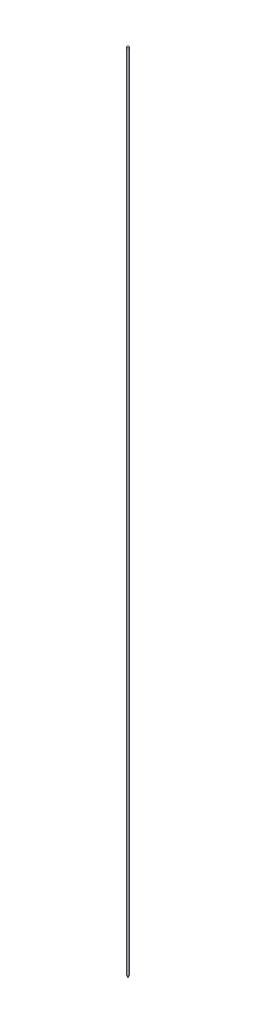
SolidWorks part; units mm, degrees
ref_plane "Alzado" through (0, 0, 0) normal (0, 0, 1) x (1, 0, 0)
ref_plane "Planta" through (0, 0, 0) normal (0, 1, 0) x (1, 0, 0)
ref_plane "Vista lateral" through (0, 0, 0) normal (1, 0, 0) x (0, 0, -1)
sketch "Croquis1" plane through (0, 0, 0) normal (0, 0, 1) x (1, 0, 0)
  line L0 (0, 11.2838) -> (0, -14.3611) construction
  line L1 (0, 138.1676) -> (1.5875, 138.1676)
  line L2 (1.5875, 138.1676) -> (1.5875, -987.2524)
  line L3 (0, -990.9565) -> (1.5875, -987.2524)
  line L4 (0, -990.9565) -> (0, 138.1676)
  dimension "D1" = 1.5875
  dimension "1000" = 1125.42
revolve "Revolución1" add sketch "Croquis1" angle 360 about L0
fillet "Redondeo1" radius 1 1 edges at (0, -987.2524, 1.5875)
